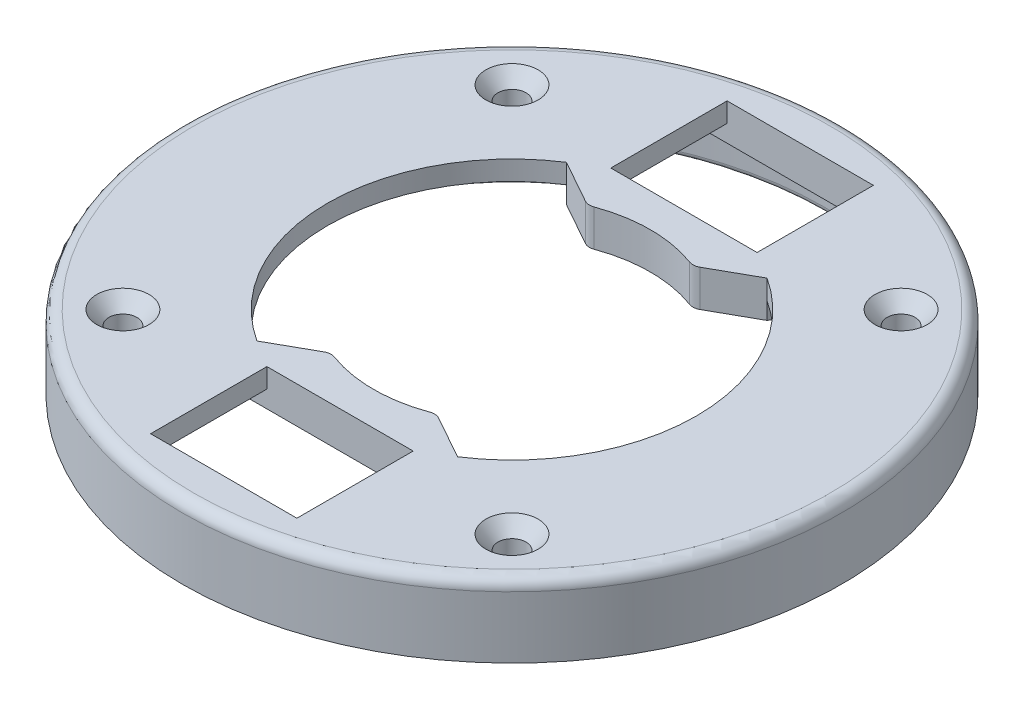
SolidWorks part; units mm, degrees
material "ABS"
ref_plane "Front Plane" through (0, 0, 0) normal (0, 0, 1) x (1, 0, 0)
ref_plane "Top Plane" through (0, 0, 0) normal (0, 1, 0) x (1, 0, 0)
ref_plane "Right Plane" through (0, 0, 0) normal (1, 0, 0) x (0, 0, -1)
sketch "Sketch1" plane through (0, 0, 0) normal (0, 1, 0) x (1, 0, 0)
  line L0 (-17.4994, 27) -> (17.4994, 27)
  line L1 (-57.5, 0) -> (57.5, 0) construction
  line L2 (-17.4994, -27) -> (17.4994, -27)
  circle A0 centre (0, 0) radius 57.5
  circle A1 centre (0, 0) radius 32.175 construction
  arc A2 (-17.4994, 27) -> (-17.4994, -27) centre (0, 0) ccw
  arc A3 (17.4994, 27) -> (17.4994, -27) centre (0, 0) cw
  dimension "D1" = 115
  dimension "D2" = 64.35
  dimension "D3" = 27
extrude "Boss-Extrude1" add sketch "Sketch1" along normal blind 6.4 contours A0 L0 A3 L2 A2
sketch "Sketch2" plane through (0, 6.4, 0) normal (0, 1, 0) x (1, 0, 0)
  line L0 (0, 57.5) -> (0, 0) construction
  line L1 (0, 0) -> (57.5, 0) construction
  line L3 (-12.7625, 50.295) -> (12.7625, 50.295)
  line L4 (-12.7625, 50.295) -> (-12.7625, 30)
  line L5 (-12.7625, 30) -> (12.7625, 30)
  line L6 (12.7625, 50.295) -> (12.7625, 30)
  line L7 (-12.7625, -30) -> (12.7625, -30)
  line L8 (12.7625, -50.295) -> (12.7625, -30)
  line L9 (-12.7625, -50.295) -> (-12.7625, -30)
  line L10 (-12.7625, -50.295) -> (12.7625, -50.295)
  circle A0 centre (0, 0) radius 57.5 construction
  dimension "D1" = 20.295
  dimension "D2" = 25.525
  dimension "D3" = 30
extrude "Cut-Extrude1" cut sketch "Sketch2" against normal through all
sketch "Sketch3" plane through (0, 0, 0) normal (0, -1, 0) x (1, 0, 0)
  line L0 (12.7625, 30) -> (-12.7625, 30) construction
  line L1 (12.7625, 50.295) -> (16.7625, 50.295)
  line L2 (12.7625, 50.295) -> (12.7625, 30)
  line L3 (12.7625, 30) -> (16.7625, 30)
  line L4 (16.7625, 50.295) -> (16.7625, 30)
  line L5 (0, 57.5) -> (0, 0) construction
  line L6 (0, 0) -> (-57.5, 0) construction
  line L7 (-12.7625, 30) -> (-16.7625, 30)
  line L8 (-16.7625, 50.295) -> (-16.7625, 30)
  line L9 (-12.7625, 50.295) -> (-12.7625, 30)
  line L10 (-12.7625, 50.295) -> (-16.7625, 50.295)
  line L11 (16.7625, -50.295) -> (16.7625, -30)
  line L12 (12.7625, -30) -> (16.7625, -30)
  line L13 (12.7625, -50.295) -> (12.7625, -30)
  line L14 (12.7625, -50.295) -> (16.7625, -50.295)
  line L15 (-12.7625, -50.295) -> (-16.7625, -50.295)
  line L16 (-12.7625, -50.295) -> (-12.7625, -30)
  line L17 (-16.7625, -50.295) -> (-16.7625, -30)
  line L18 (-12.7625, -30) -> (-16.7625, -30)
  circle A0 centre (0, 0) radius 57.5 construction
  dimension "D1" = 4
extrude "Cut-Extrude2" cut sketch "Sketch3" against normal blind 3
sketch "Sketch4" plane through (0, 0, 0) normal (0, -1, 0) x (1, 0, 0)
  line L0 (-17.4994, 27) -> (0, 0) construction
  line L1 (0, 0) -> (-17.4994, -27) construction
  line L2 (0, 57.5) -> (0, -57.5) construction
  line L3 (-19.7702, 30.5035) -> (-17.4994, 27)
  line L4 (-19.7702, -30.5035) -> (-17.4994, -27)
  line L5 (19.7702, -30.5035) -> (17.4994, -27)
  line L6 (19.7702, 30.5035) -> (17.4994, 27)
  circle A0 centre (0, 0) radius 57.5 construction
  arc A1 (-19.7702, 30.5035) -> (-19.7702, -30.5035) centre (0, 0) ccw
  arc A2 (-17.4994, 27) -> (-17.4994, -27) centre (0, 0) ccw construction
  arc A3 (-17.4994, 27) -> (-17.4994, -27) centre (0, 0) ccw
  arc A4 (17.4994, -27) -> (17.4994, 27) centre (0, 0) ccw construction
  arc A5 (17.4994, -27) -> (17.4994, 27) centre (0, 0) ccw
  arc A6 (17.4994, 27) -> (17.4994, -27) centre (0, 0) cw
  arc A7 (19.7702, 30.5035) -> (19.7702, -30.5035) centre (0, 0) cw
  arc M11 (-17.4994, -27) -> (-17.4994, 27) centre (0, 0) cw
  arc M13 (17.4994, 27) -> (17.4994, -27) centre (0, 0) cw
  dimension "D1" = 4.175
extrude "Cut-Extrude3" cut sketch "Sketch4" against normal blind 3 contours L3 A1 L4 M11 | A7 L6 L5 M13
sketch "Sketch5" plane through (0, 0, 0) normal (0, -1, 0) x (1, 0, 0)
  line L0 (0, 57.5) -> (0, 0) construction
  line L1 (0, 0) -> (-57.5, 0) construction
  line L2 (0, 0) -> (-40.6586, 40.6586) construction
  line L3 (-57.5, 0) -> (-40.6586, 40.6586) construction
  line L4 (-40.6586, 40.6586) -> (0, 57.5) construction
  circle A0 centre (0, 0) radius 57.5 construction
  circle A1 centre (-33.9411, 33.9411) radius 1
  circle A2 centre (33.9411, 33.9411) radius 1
  circle A3 centre (33.9411, -33.9411) radius 1
  circle A4 centre (-33.9411, -33.9411) radius 1
  point P18 (0, 0)
  dimension "D1" = 2
  dimension "D2" = 48
  dimension "D3" = 4
extrude "Cut-Extrude4" cut sketch "Sketch5" against normal through all
hole_wizard "CSK for #8 Flat Head Socket Cap Screw1" positions "Sketch7" profile "Sketch6" countersink size "#8" standard "ANSI Inch" end condition through all
sketch "Sketch7" plane through (0, 6.4, 0) normal (0, 1, 0) x (1, 0, 0)
  point P0 (-33.9411, 33.9411)
  point P3 (33.9411, 33.9411)
  point P6 (33.9411, -33.9411)
  point P9 (-33.9411, -33.9411)
sketch "Sketch6" plane through (-33.9411, 6.4, -33.9411) normal (1, 0, 0) x (0, 0, 1)
  line L0 (0, 0) -> (0, 6.4)
  line L1 (0, 6.4) -> (2.4574, 6.4)
  line L2 (2.4574, 6.4) -> (2.4574, 2.4179)
  line L3 (2.4574, 2.4179) -> (4.5593, 0)
  line L5 (4.5593, 0) -> (0, 0)
  line L6 (-2.4575, 2.4179) -> (-4.5593, 0) construction
  line L11 (0, -6.35) -> (0, 107.95) construction
  dimension "Thru Hole Dia." = 4.9149
  dimension "Thru Hole Depth" = 6.4
  dimension "Near C'Sink Dia." = 9.1186
  dimension "Near C'Sink Angle" = 82
sketch "Sketch9" plane through (0, 6.4, 0) normal (0, 1, 0) x (1, 0, 0)
  line L0 (0, 0) -> (28.0688, 15.7281) construction
  line L1 (17.4994, 27) -> (-32.1643, -0.8286) construction
  line L2 (0, 0) -> (0, 27) construction
  line L3 (-17.4994, 27) -> (17.4994, 27) construction
  line L4 (-17.4994, 27) -> (17.4994, 27)
  line L5 (17.4994, 27) -> (9.1789, 22.3377)
  line L6 (-17.4994, 27) -> (-9.1789, 22.3377)
  line L7 (0, 0) -> (24.15, 0) construction
  line L8 (17.4994, -27) -> (9.1789, -22.3377)
  line L9 (-17.4994, -27) -> (17.4994, -27)
  line L10 (-17.4994, -27) -> (-9.1789, -22.3377)
  arc A0 (17.4994, -27) -> (17.4994, 27) centre (0, 0) ccw construction
  arc A1 (-17.4994, 27) -> (-17.4994, -27) centre (0, 0) ccw construction
  circle A2 centre (0, 0) radius 24.15 construction
  arc A3 (-9.1789, 22.3377) -> (9.1789, 22.3377) centre (0, 0) cw
  arc A4 (-9.1789, -22.3377) -> (9.1789, -22.3377) centre (0, 0) ccw
  dimension "D2" = 48.3
  dimension "D1" = 15
extrude "Boss-Extrude2" add sketch "Sketch9" against normal up to surface (6.4 mm away) up to face at (-33.9411, 0, -31.4837)
fillet "Fillet1" radius 2 5 edges at (9.1789, 3.2, 22.3377) (-9.1789, 3.2, 22.3377) (9.1789, 3.2, -22.3377) (-9.1789, 3.2, -22.3377) (0, 6.4, 57.5)
sketch "Sketch10" plane through (0, 0, 0) normal (0, -1, 0) x (1, 0, 0)
  circle A0 centre (0, 0) radius 57.5 construction
  circle A1 centre (0, 0) radius 57.5
  circle A2 centre (0, 0) radius 54.5
  dimension "D1" = 3
extrude "Boss-Extrude3" add sketch "Sketch10" along normal blind 6.375
fillet "Fillet2" radius 1 1 edges at (0, -6.375, -54.5)
